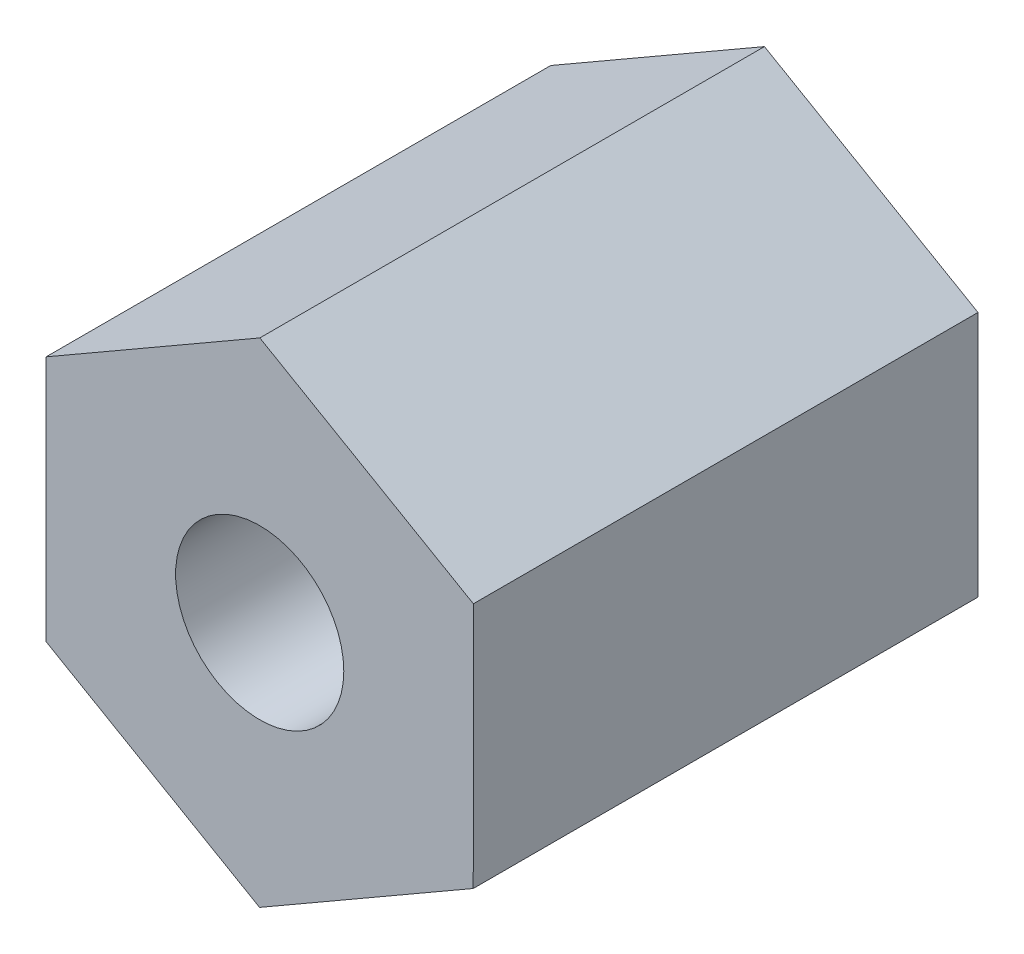
SolidWorks part; units mm, degrees
ref_plane "Alzado" through (0, 0, 0) normal (0, 0, 1) x (1, 0, 0)
ref_plane "Planta" through (0, 0, 0) normal (0, 1, 0) x (1, 0, 0)
ref_plane "Vista lateral" through (0, 0, 0) normal (1, 0, 0) x (0, 0, -1)
sketch "Croquis1" plane through (0, 0, 0) normal (0, 0, 1) x (1, 0, 0)
  line L1 (6.3479, -3.6698) -> (6.3521, 3.6625)
  line L2 (6.3521, 3.6625) -> (0.0042, 7.3323)
  line L3 (0.0042, 7.3323) -> (-6.3479, 3.6698)
  line L4 (-6.3479, 3.6698) -> (-6.3521, -3.6625)
  line L5 (-6.3521, -3.6625) -> (-0.0042, -7.3323)
  line L6 (-0.0042, -7.3323) -> (6.3479, -3.6698)
  circle A0 centre (0, 0) radius 6.35 construction
  circle A1 centre (0, 0) radius 2.5
  dimension "D2" = 5
  dimension "D1" = 12.7
extrude "Saliente-Extruir1" add sketch "Croquis1" along normal blind 15
